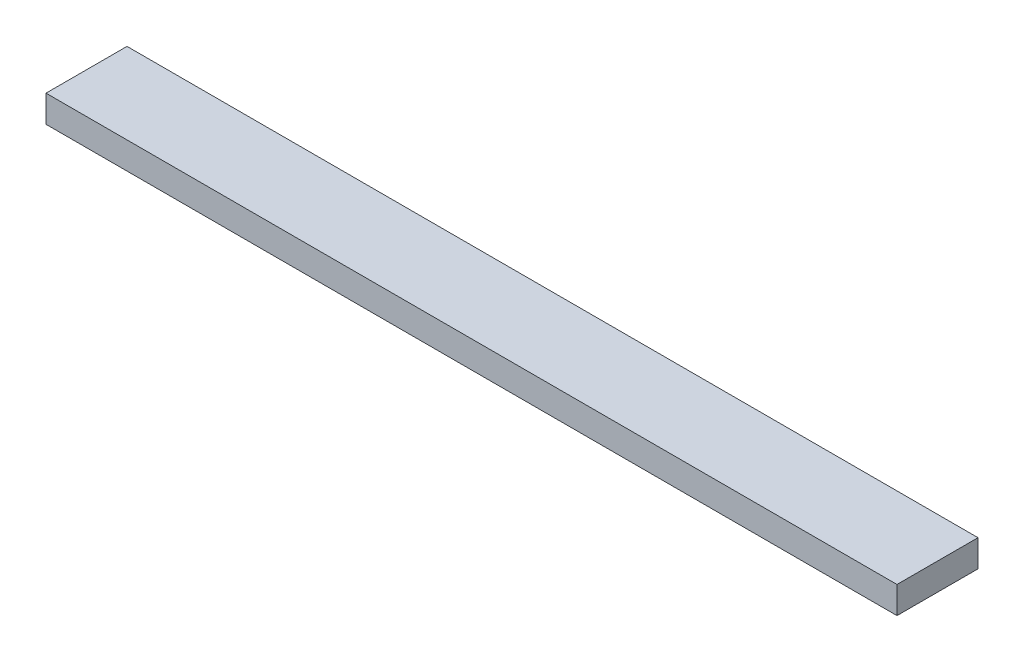
SolidWorks part; units mm, degrees
ref_plane "Front Plane" through (0, 0, 0) normal (0, 0, 1) x (1, 0, 0)
ref_plane "Top Plane" through (0, 0, 0) normal (0, 1, 0) x (1, 0, 0)
ref_plane "Right Plane" through (0, 0, 0) normal (1, 0, 0) x (0, 0, -1)
sketch "Sketch1" plane through (0, 0, 0) normal (1, 0, 0) x (0, 0, -1)
  line L1 (0, 0) -> (38.1, 0)
  line L2 (0, 0) -> (0, 12.7)
  line L3 (0, 12.7) -> (38.1, 12.7)
  line L4 (38.1, 0) -> (38.1, 12.7)
  dimension "D1" = 38.1
  dimension "D2" = 12.7
extrude "Boss-Extrude1" add sketch "Sketch1" along normal blind 400.2
